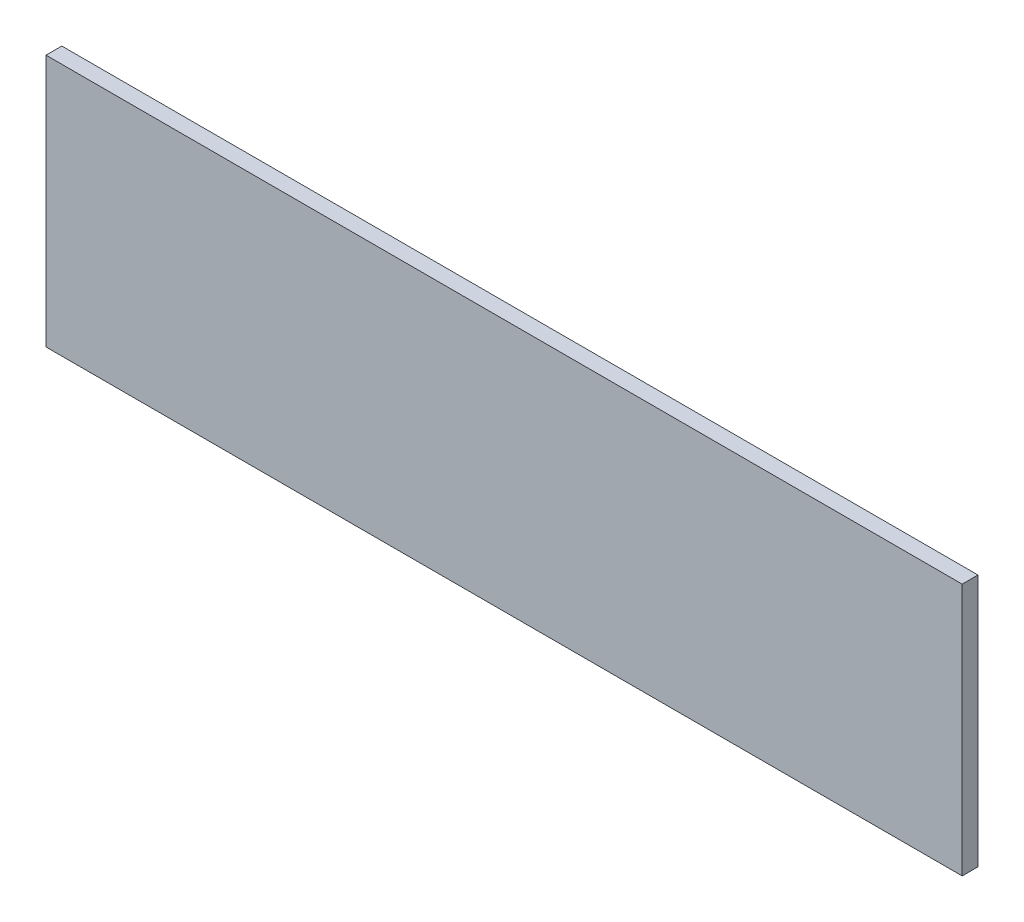
SolidWorks part; units mm, degrees
ref_plane "Front Plane" through (0, 0, 0) normal (0, 0, 1) x (1, 0, 0)
ref_plane "Top Plane" through (0, 0, 0) normal (0, 1, 0) x (1, 0, 0)
ref_plane "Right Plane" through (0, 0, 0) normal (1, 0, 0) x (0, 0, -1)
sketch "Sketch2" plane through (0, 0, 0) normal (0, 0, 1) x (1, 0, 0)
  line L1 (-92.075, -25.4) -> (92.075, -25.4)
  line L2 (-92.075, -25.4) -> (-92.075, 25.4)
  line L3 (-92.075, 25.4) -> (92.075, 25.4)
  line L4 (92.075, -25.4) -> (92.075, 25.4)
  line L5 (-92.075, -25.4) -> (92.075, 25.4) construction
  line L6 (-92.075, 25.4) -> (92.075, -25.4) construction
  point P0 (0, 0)
  dimension "D1" = 184.15
  dimension "D2" = 50.8
extrude "Boss-Extrude1" add sketch "Sketch2" along normal mid plane 3.175
